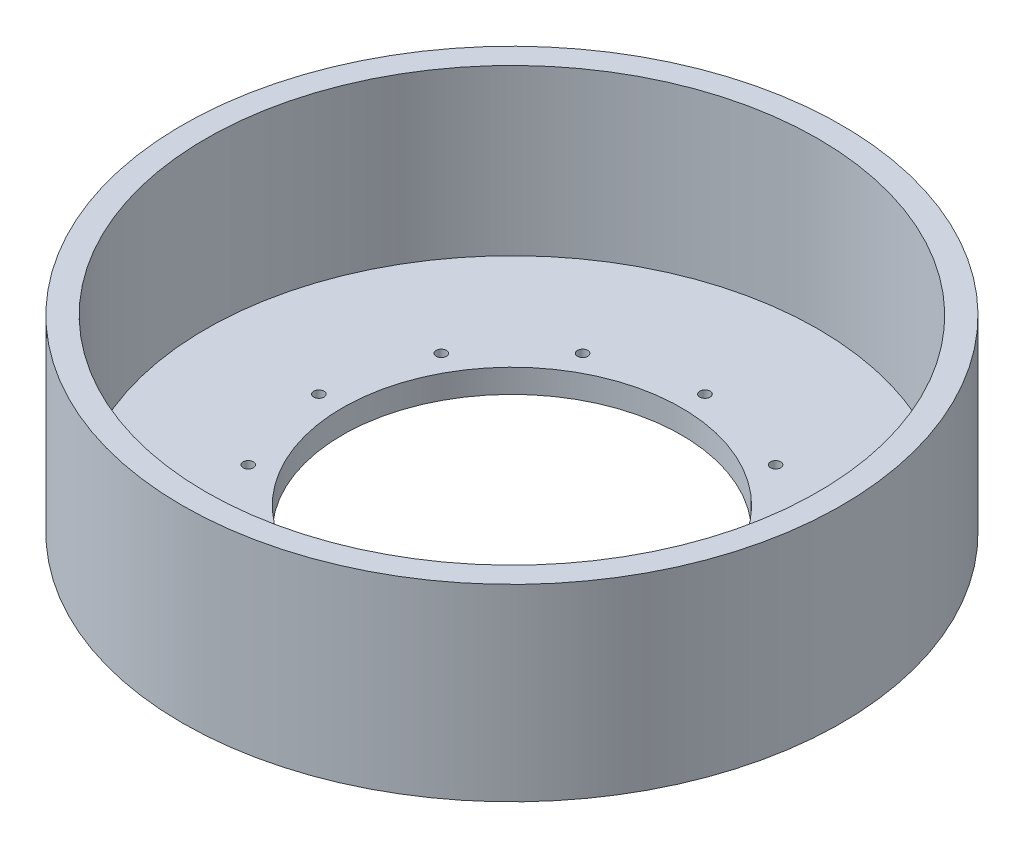
SolidWorks part; units mm, degrees
ref_plane "Front Plane" through (0, 0, 0) normal (0, 0, 1) x (1, 0, 0)
ref_plane "Top Plane" through (0, 0, 0) normal (0, 1, 0) x (1, 0, 0)
ref_plane "Right Plane" through (0, 0, 0) normal (1, 0, 0) x (0, 0, -1)
sketch "Sketch1" plane through (0, 0, 0) normal (0, 1, 0) x (1, 0, 0)
  circle A0 centre (0, 0) radius 88.9
  dimension "D1" = 177.8
extrude "Boss-Extrude1" add sketch "Sketch1" along normal blind 50.8 contours A0
sketch "Sketch2" plane through (0, 50.8, 0) normal (0, 1, 0) x (1, 0, 0)
  circle A0 centre (0, 0) radius 88.9 construction
  circle A1 centre (0, 0) radius 88.9 construction
  circle A2 centre (0, 0) radius 82.55
  dimension "D1" = 6.35
extrude "Cut-Extrude1" cut sketch "Sketch2" against normal blind 44.45
sketch "Sketch3" plane through (0, 6.35, 0) normal (0, 1, 0) x (1, 0, 0)
  circle A0 centre (0, 0) radius 45.72
  circle A1 centre (0, 0) radius 52.07 construction
  circle A2 centre (0, 52.07) radius 1.397
  circle A3 centre (26.035, 45.0939) radius 1.397
  circle A4 centre (45.0939, 26.035) radius 1.397
  circle A5 centre (52.07, 0) radius 1.397
  circle A6 centre (45.0939, -26.035) radius 1.397
  circle A7 centre (26.035, -45.0939) radius 1.397
  circle A8 centre (0, -52.07) radius 1.397
  circle A9 centre (-26.035, -45.0939) radius 1.397
  circle A10 centre (-45.0939, -26.035) radius 1.397
  circle A11 centre (-52.07, 0) radius 1.397
  circle A12 centre (-45.0939, 26.035) radius 1.397
  circle A13 centre (-26.035, 45.0939) radius 1.397
  point P31 (0, 0)
  dimension "D1" = 91.44
  dimension "D3" = 2.794
  dimension "D2" = 6.35
  dimension "D4" = 12
extrude "Cut-Extrude2" cut sketch "Sketch3" against normal through all
